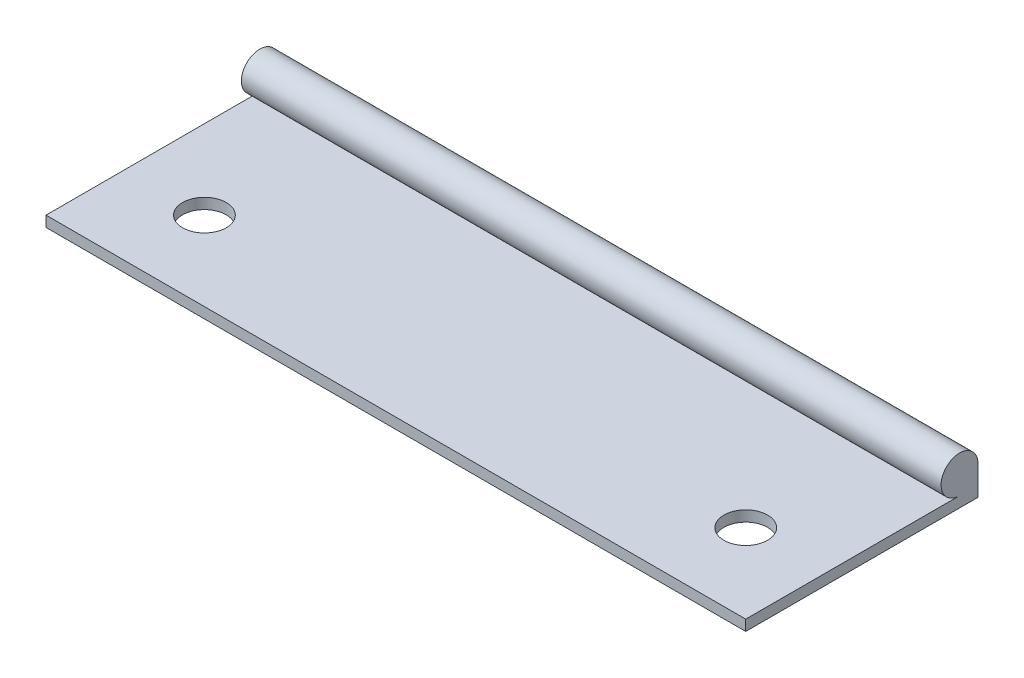
SolidWorks part; units mm, degrees
ref_plane "Front" through (0, 0, 0) normal (0, 0, 1) x (1, 0, 0)
ref_plane "Top" through (0, 0, 0) normal (0, 1, 0) x (1, 0, 0)
ref_plane "Right" through (0, 0, 0) normal (1, 0, 0) x (0, 0, -1)
sketch "草图1" plane through (0, 0, 0) normal (1, 0, 0) x (0, 0, -1)
  line L0 (0, 0) -> (0, 1.1)
  line L1 (0, 1.1) -> (19, 1.1)
  line L2 (0, 0) -> (19, 0)
  line L3 (19, 0) -> (19, 10.8121) construction
  line L4 (19, 1.1) -> (22, 1.1)
  line L5 (19, 0) -> (23.9, 0)
  line L6 (23.9, 0) -> (23.9, 3)
  circle A0 centre (22, 3) radius 3 construction
  circle A1 centre (22, 3) radius 1.9
  dimension "D3" = 6
  dimension "D1" = 1.1
  dimension "D2" = 19
extrude "凸台-拉伸1" add sketch "草图1" along normal blind 72 contours A1 | A1 L4 L1 L0 L2 L5 L6
sketch "草图2" plane through (0, 1.1, 0) normal (0, 1, 0) x (1, 0, 0)
  line L0 (0, 8.15) -> (72, 8.15) construction
  line L1 (0, 0) -> (0, 22) construction
  line L2 (72, 0) -> (72, 22) construction
  line L3 (72, 0) -> (0, 0) construction
  circle A0 centre (8.15, 8.15) radius 2.25
  circle A1 centre (63.85, 8.15) radius 2.25
  dimension "D1" = 4.5
  dimension "D2" = 4.5
  dimension "D3" = 8.15
  dimension "D4" = 8.15
  dimension "D5" = 8.15
extrude "切除-拉伸1" cut sketch "草图2" against normal through all
